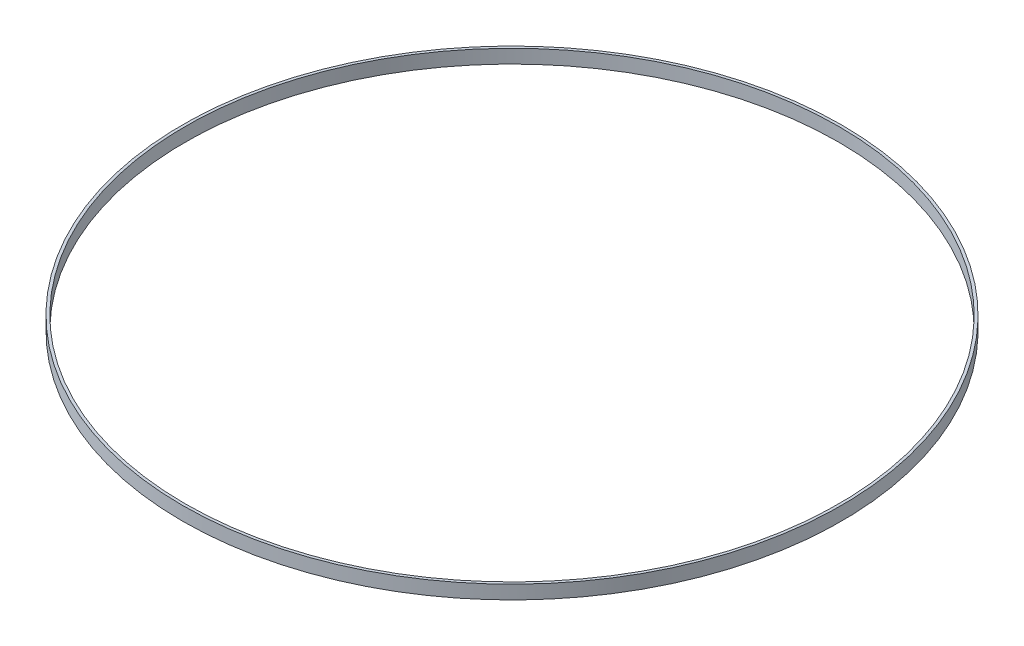
SolidWorks part; units mm, degrees
ref_plane "Front Plane" through (0, 0, 0) normal (0, 0, 1) x (1, 0, 0)
ref_plane "Top Plane" through (0, 0, 0) normal (0, 1, 0) x (1, 0, 0)
ref_plane "Right Plane" through (0, 0, 0) normal (1, 0, 0) x (0, 0, -1)
sketch "Sketch1" plane through (0, 0, 0) normal (0, 1, 0) x (1, 0, 0)
  circle A0 centre (0, 0) radius 30.5943
  circle A1 centre (0, 0) radius 30.3403
  dimension "D1" = 61.1886
  dimension "D2" = 60.6806
extrude "Boss-Extrude1" add sketch "Sketch1" along normal blind 1.27
